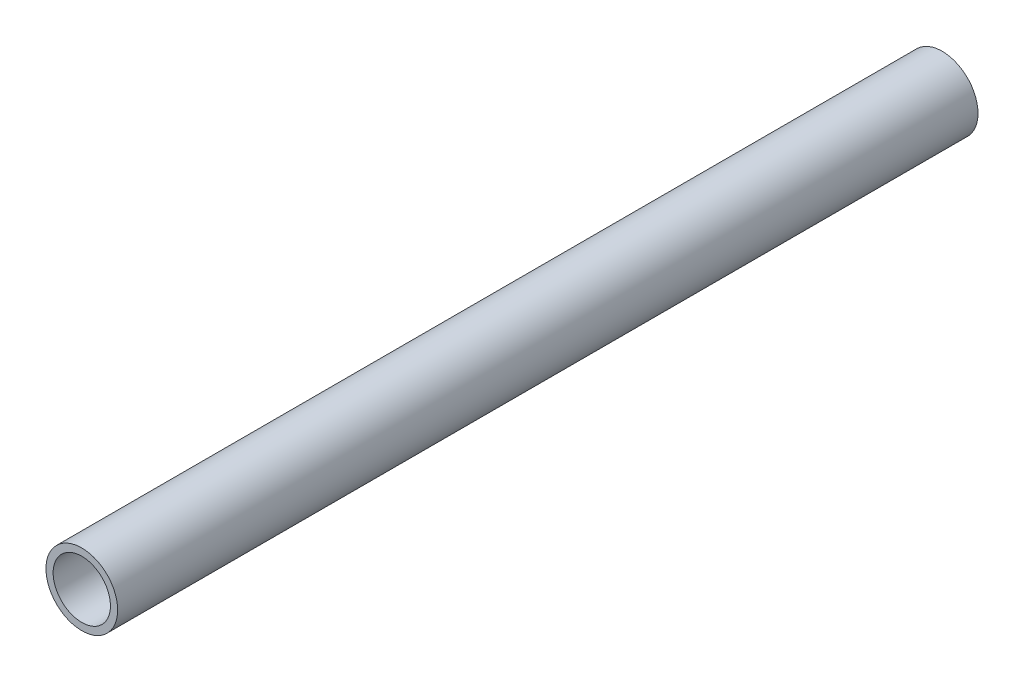
SolidWorks part; units mm, degrees
ref_plane "Front Plane" through (0, 0, 0) normal (0, 0, 1) x (1, 0, 0)
ref_plane "Top Plane" through (0, 0, 0) normal (0, 1, 0) x (1, 0, 0)
ref_plane "Right Plane" through (0, 0, 0) normal (1, 0, 0) x (0, 0, -1)
sketch "Sketch1" plane through (0, 0, 0) normal (0, 0, 1) x (1, 0, 0)
  circle A0 centre (0, 0) radius 1.25
extrude "Boss-Extrude1" add sketch "Sketch1" along normal blind 30
sketch "Sketch4" plane through (0, 0, 0) normal (0, 0, -1) x (-1, 0, 0)
  circle A3 centre (0, 0) radius 1
extrude "Cut-Extrude1" cut sketch "Sketch4" against normal blind 30
sketch3d "3DSketch1"
  circle A0 centre (0, 0, 0) radius 1 construction
  point P2 (0, 0, -1)
sketch "Sketch5" plane through (0, 0, 30) normal (0, 0, 1) x (1, 0, 0)
  line L0 (1, 0) -> (-1, 0)
  line L1 (1, 0.159) -> (1, -0.161)
  circle A0 centre (0, 0) radius 1 construction
  circle A1 centre (0.9, 0) radius 0.1
